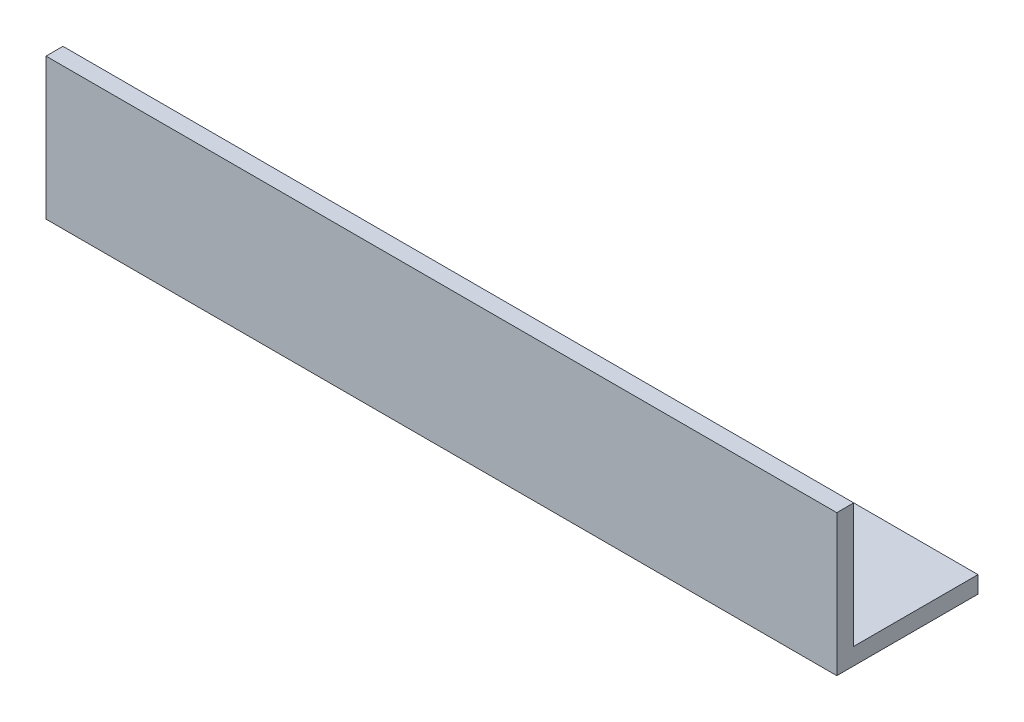
SolidWorks part; units mm, degrees
ref_plane "Спереди" through (0, 0, 0) normal (0, 0, 1) x (1, 0, 0)
ref_plane "Сверху" through (0, 0, 0) normal (0, 1, 0) x (1, 0, 0)
ref_plane "Справа" through (0, 0, 0) normal (1, 0, 0) x (0, 0, -1)
sketch "Эскиз1" plane through (0, 0, 0) normal (1, 0, 0) x (0, 0, -1)
  line L0 (0, 25) -> (0, 0)
  line L1 (0, 0) -> (25, 0)
  line L2 (25, 0) -> (25, 3)
  line L3 (25, 3) -> (3, 3)
  line L4 (3, 3) -> (3, 25)
  line L5 (3, 25) -> (0, 25)
extrude "Бобышка-Вытянуть1" add sketch "Эскиз1" along normal blind 140
